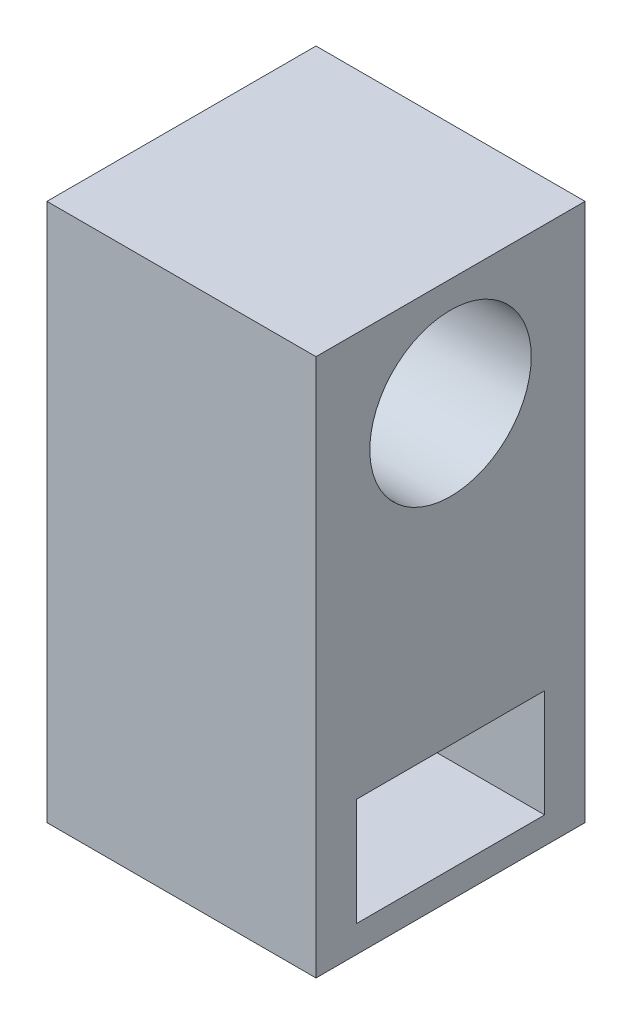
SolidWorks part; units mm, degrees
ref_plane "前视基准面" through (0, 0, 0) normal (0, 0, 1) x (1, 0, 0)
ref_plane "上视基准面" through (0, 0, 0) normal (0, 1, 0) x (1, 0, 0)
ref_plane "右视基准面" through (0, 0, 0) normal (1, 0, 0) x (0, 0, -1)
sketch "草图1" plane through (0, 0, 0) normal (0, 0, 1) x (1, 0, 0)
  line L0 (-58.7629, 70.1031) -> (-58.7629, -129.8969)
  line L1 (41.2371, -129.8969) -> (41.2371, 70.1031)
  line L2 (41.2371, 70.1031) -> (-58.7629, 70.1031)
  line L3 (-58.7629, -129.8969) -> (41.2371, -129.8969)
  dimension "D1" = 100
  dimension "D2" = 200
extrude "凸台-拉伸1" add sketch "草图1" along normal blind 100
sketch "草图2" plane through (41.2371, 0, 0) normal (1, 0, 0) x (0, 0, -1)
  line L4 (0, -129.8969) -> (0, 70.1031) construction
  line L5 (-85, -79.8969) -> (-85, -119.8969)
  line L6 (-85, -119.8969) -> (-15, -119.8969)
  line L7 (-15, -119.8969) -> (-15, -79.8969)
  line L8 (-15, -79.8969) -> (-85, -79.8969)
  line L9 (-100, 70.1031) -> (0, 70.1031) construction
  line L10 (-100, -129.8969) -> (-100, 70.1031) construction
  line L11 (-100, -129.8969) -> (0, -129.8969) construction
  circle A0 centre (-50, 30.1031) radius 30
  point P4 (0, 0)
  dimension "D3" = 60
  dimension "D1" = 50
  dimension "D2" = 40
  dimension "D4" = 40
  dimension "D5" = 70
  dimension "D6" = 15
  dimension "D7" = 10
extrude "切除-拉伸1" cut sketch "草图2" against normal through all
